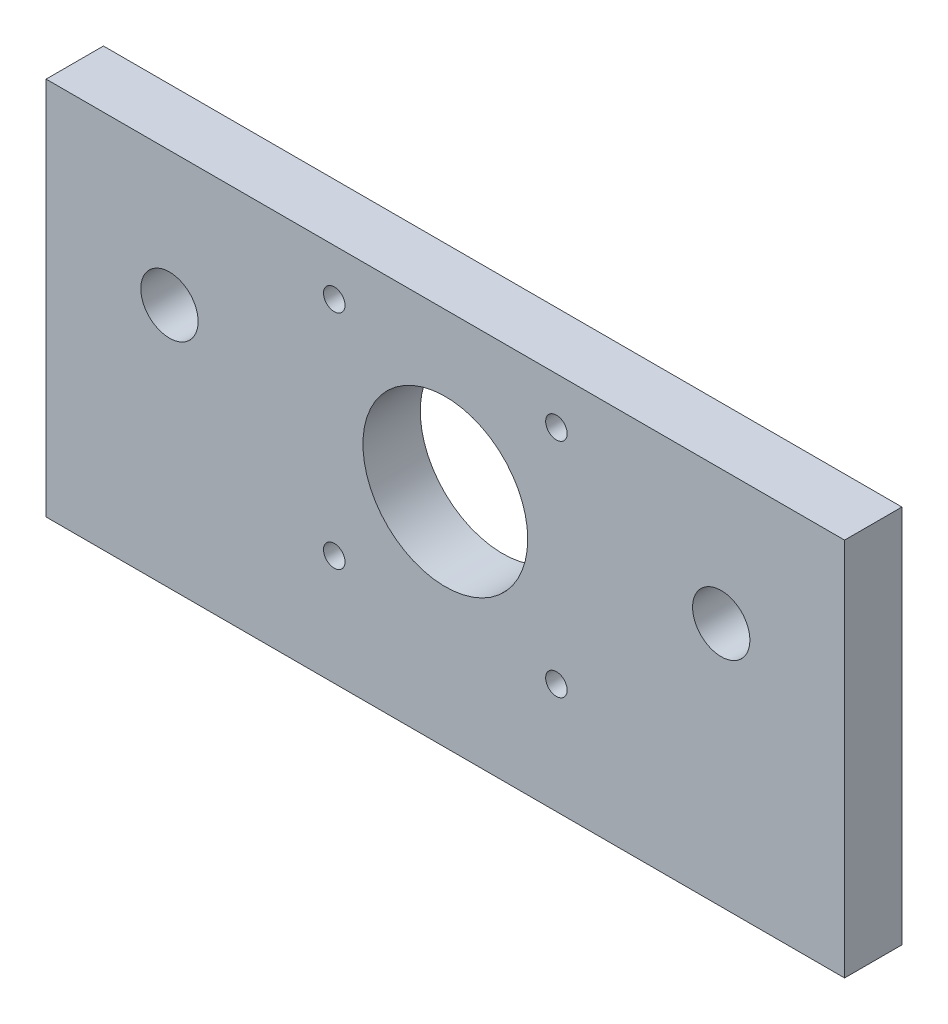
SolidWorks part; units mm, degrees
ref_plane "Front" through (0, 0, 0) normal (0, 0, 1) x (1, 0, 0)
ref_plane "Top" through (0, 0, 0) normal (0, 1, 0) x (1, 0, 0)
ref_plane "Right" through (0, 0, 0) normal (1, 0, 0) x (0, 0, -1)
sketch "Sketch1" plane through (0, 0, 0) normal (0, 0, 1) x (1, 0, 0)
  line L0 (-17.7167, -24.7168) -> (17.2833, -24.7168)
  line L1 (-55.9296, 11.2832) -> (55.4962, 11.2832)
  line L2 (-55.9296, 11.2832) -> (-55.9296, -36.5579)
  line L3 (55.4962, 11.2832) -> (55.4962, -41.6379)
  line L4 (55.4962, -41.6379) -> (-55.9296, -41.6379)
  line L5 (-55.9296, -41.6379) -> (-55.9296, -36.5579)
  circle A0 centre (38.2833, -7.4168) radius 4
  circle A1 centre (-0.2167, -10.7168) radius 5
  circle A2 centre (-38.7167, -7.4168) radius 4
extrude "Boss-Extrude1" add sketch "Sketch1" along normal blind 8
sketch "Sketch2" plane through (0, 0, 8) normal (0, 0, 1) x (1, 0, 0)
  line L0 (-15.7167, 4.7832) -> (-14.656, 3.7225) construction
  line L1 (15.2833, 4.7832) -> (14.2227, 3.7225) construction
  line L2 (-15.7167, -26.2168) -> (-14.2167, -26.2168) construction
  line L3 (15.2833, -26.2168) -> (15.2833, -24.7168) construction
  line L4 (15.2833, 4.7832) -> (13.7833, 4.7832) construction
  line L5 (-15.7167, 4.7832) -> (-15.7167, 3.2832) construction
  line L6 (-14.2167, 4.7832) -> (-15.7167, 4.7832) construction
  line L8 (-15.7167, -24.7168) -> (-15.7167, -26.2168) construction
  line L9 (-14.656, -25.1561) -> (-15.7167, -26.2168) construction
  line L10 (13.7833, -26.2168) -> (15.2833, -26.2168) construction
  line L11 (14.2227, -25.1561) -> (15.2833, -26.2168) construction
  line L12 (15.2833, 3.2832) -> (15.2833, 4.7832) construction
  circle A0 centre (-0.2167, -10.7168) radius 11.5
  circle A1 centre (-15.7167, -26.2168) radius 1.5
  circle A2 centre (15.2833, -26.2168) radius 1.5
  circle A3 centre (-15.7167, 4.7832) radius 1.5
  circle A4 centre (15.2833, 4.7832) radius 1.5
  circle A5 centre (-0.2167, -10.7168) radius 5 construction
extrude "Cut-Extrude1" cut sketch "Sketch2" against normal through all
